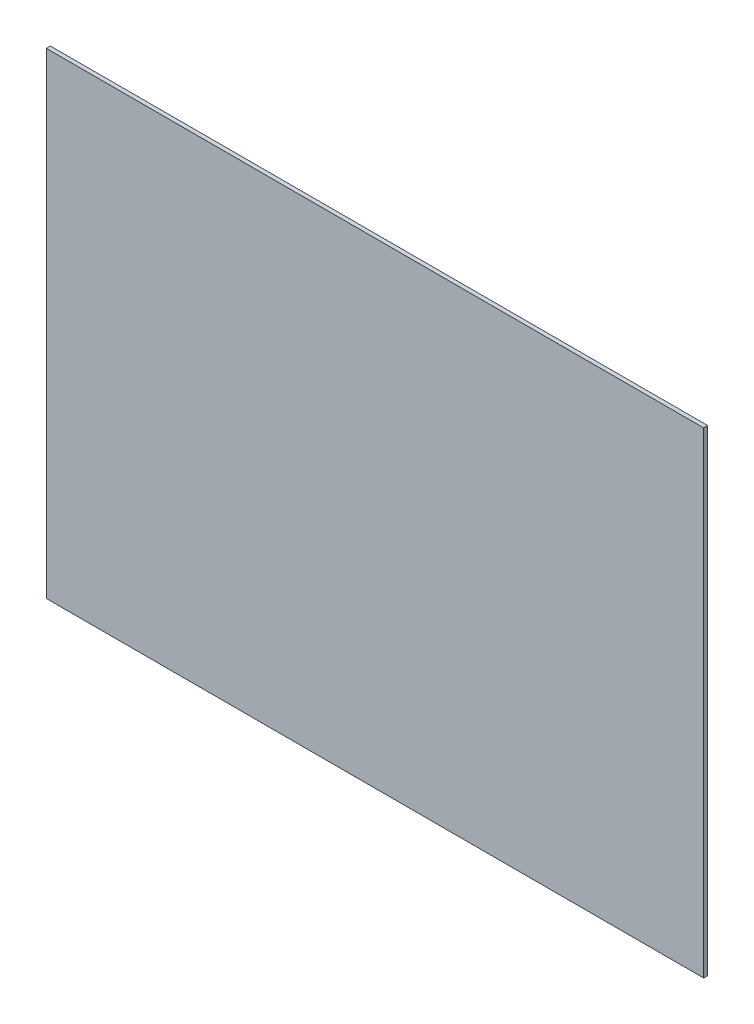
SolidWorks part; units mm, degrees
ref_plane "Front Plane" through (0, 0, 0) normal (0, 0, 1) x (1, 0, 0)
ref_plane "Top Plane" through (0, 0, 0) normal (0, 1, 0) x (1, 0, 0)
ref_plane "Right Plane" through (0, 0, 0) normal (1, 0, 0) x (0, 0, -1)
sketch "Sketch1" plane through (0, 0, 0) normal (0, 0, 1) x (1, 0, 0)
  line L0 (-482.6, 329.5) -> (482.6, 329.5) construction
  line L1 (-454.6, -329.5) -> (454.6, -329.5)
  line L2 (-454.6, -329.5) -> (-454.6, 329.5)
  line L3 (-454.6, 329.5) -> (454.6, 329.5)
  line L4 (454.6, -329.5) -> (454.6, 329.5)
  line L5 (-454.6, -329.5) -> (454.6, 329.5) construction
  line L6 (-454.6, 329.5) -> (454.6, -329.5) construction
  line L7 (-454.6, -317.5) -> (-454.6, 317.5) construction
  point P0 (0, 0)
extrude "Boss-Extrude1" add sketch "Sketch1" along normal mid plane 5.588
